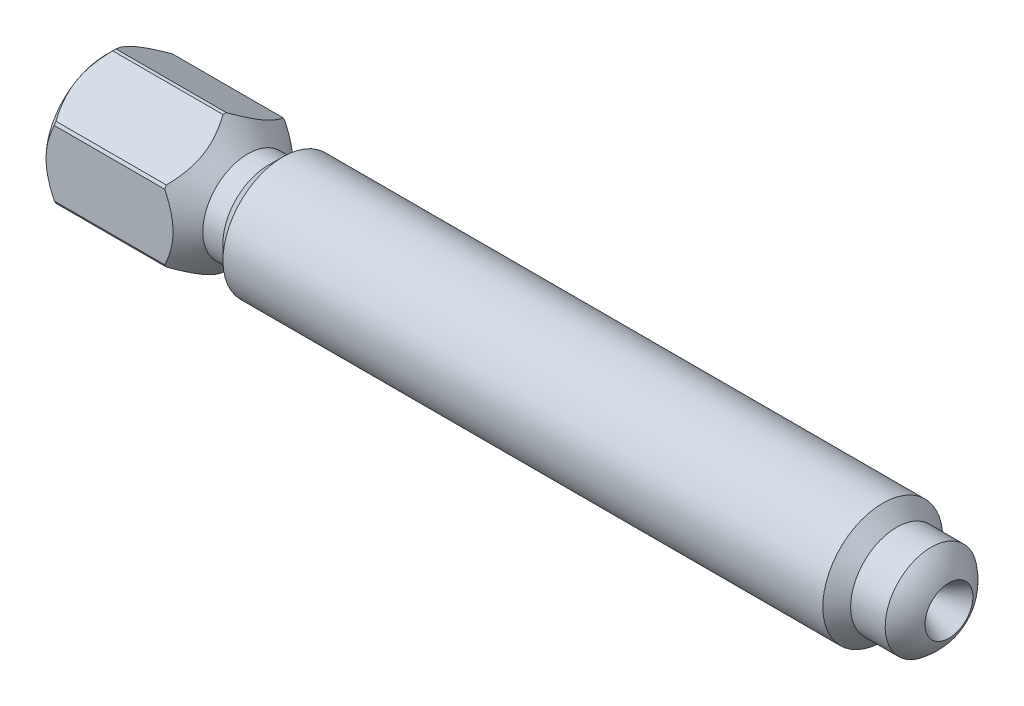
SolidWorks part; units mm, degrees
material "NITRONIC 60"
ref_plane "Plane1" through (0, 0, 0) normal (0, 0, 1) x (1, 0, 0)
ref_plane "Plane2" through (0, 0, 0) normal (0, 1, 0) x (1, 0, 0)
ref_plane "Plane3" through (0, 0, 0) normal (1, 0, 0) x (0, 0, -1)
sketch "Sketch1" plane through (0, 0, 0) normal (0, 0, 1) x (1, 0, 0)
  line L0 (1.1636, 0) -> (0, 0) construction
  line L1 (-4.7308, 3.9687) -> (-44.45, 3.9687)
  line L2 (-56.1657, 3.9687) -> (-56.1657, 0)
  line L3 (0, 0) -> (-56.1657, 0)
  line L4 (1.1636, 0) -> (-0.8914, 2.449) construction
  line L5 (1.1636, 0) -> (-0.8914, -2.449) construction
  line L6 (-4.7308, 3.9687) -> (-3.81, 3.048)
  line L7 (-3.81, 3.048) -> (-1.524, 3.048)
  line L8 (-48.5458, 4.7625) -> (-46.7677, 2.9845)
  line L9 (-48.5458, 4.7625) -> (-55.372, 4.7625)
  line L10 (-55.372, 4.7625) -> (-56.1657, 3.9687)
  line L11 (-44.45, 3.9687) -> (-45.4342, 2.9845)
  line L12 (-46.7677, 2.9845) -> (-45.4342, 2.9845)
  line L13 (-47.752, 3.9687) -> (-47.752, 2.9845) construction
  arc A0 (0, 0) -> (-1.524, 3.048) centre (-3.81, 0) ccw
  dimension "D1" = 3.81
  dimension "D2" = 44.45
  dimension "D3" = 7.9375
  dimension "D4" = 100
  dimension "D5" = 6.096
  dimension "D6" = 45
  dimension "D7" = 3.81
  dimension "D8" = 9.398
  dimension "D9" = 9.525
  dimension "D10" = 3.302
  dimension "D11" = 5.969
revolve "Revolve1" add sketch "Sketch1" angle 360 about L0
sketch "Sketch2" plane through (-56.1657, 0, 0) normal (-1, 0, 0) x (0, 0, 1)
  line L1 (0, -4.5827) -> (3.9687, -2.2914)
  line L2 (3.9687, -2.2914) -> (3.9687, 2.2914)
  line L3 (3.9687, 2.2914) -> (0, 4.5827)
  line L4 (0, 4.5827) -> (-3.9688, 2.2914)
  line L5 (-3.9688, 2.2914) -> (-3.9688, -2.2914)
  line L6 (-3.9688, -2.2914) -> (0, -4.5827)
  circle A0 centre (0, 0) radius 3.9688 construction
  dimension "D1" = 7.9375
extrude "Cut-Extrude1" cut sketch "Sketch2" against normal through all flip side to cut
sketch "Sketch3" plane through (-56.1657, 0, 0) normal (-1, 0, 0) x (0, 0, 1)
  circle A0 centre (0, 0) radius 4.5212
  dimension "D1" = 9.0424
extrude "Cut-Extrude2" cut sketch "Sketch3" against normal through all flip side to cut
sketch "Sketch4" plane through (0, 0, 0) normal (0, 0, 1) x (1, 0, 0)
  line L0 (1.1636, 0) -> (0, 0) construction
  line L1 (1.1636, 0) -> (0, 0) construction
  line L2 (-0.3465, 1.5875) -> (-2.065, 0.5953)
  line L3 (-2.065, 0.5953) -> (-3.2556, 0.5953)
  line L4 (-3.2556, 0.5953) -> (-3.5993, 0)
  line L5 (-3.5993, 0) -> (0, 0)
  line L6 (-0.3465, -1.5875) -> (-2.065, -0.5953) construction
  line L7 (-3.2556, -0.5953) -> (-3.5993, 0) construction
  line L8 (-56.1657, 0) -> (-52.9129, 0)
  line L9 (-56.1657, 3.437) -> (-56.1657, 0) construction
  line L10 (-56.1657, 1.5875) -> (-56.1657, 0)
  line L11 (-56.1657, 1.5875) -> (-54.4472, 0.5953)
  line L12 (-54.4472, 0.5953) -> (-53.2566, 0.5953)
  line L13 (-53.2566, 0.5953) -> (-52.9129, 0)
  arc A0 (0, 0) -> (-1.524, 3.048) centre (-3.81, 0) ccw construction
  arc A1 (0, 0) -> (-0.3465, 1.5875) centre (-3.81, 0) ccw
  dimension "D1" = 60
  dimension "D2" = 3.175
  dimension "D3" = 1.1906
  dimension "D4" = 1.1906
  dimension "D5" = 120
revolve "Cut-Revolve1" cut sketch "Sketch4" angle 360 about L1
